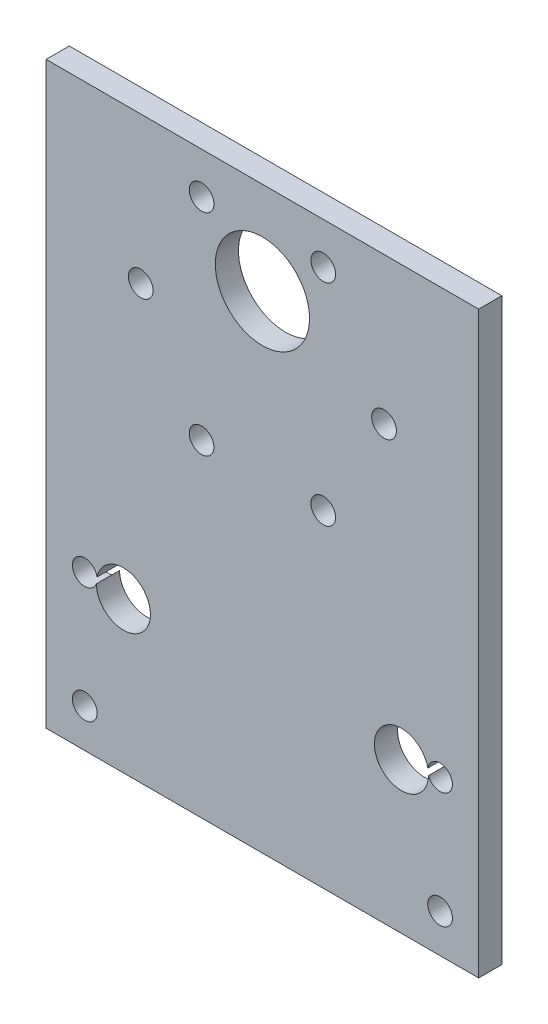
SolidWorks part; units mm, degrees
ref_plane "正面" through (0, 0, 0) normal (0, 0, 1) x (1, 0, 0)
ref_plane "平面" through (0, 0, 0) normal (0, 1, 0) x (1, 0, 0)
ref_plane "右側面" through (0, 0, 0) normal (1, 0, 0) x (0, 0, -1)
sketch "ｽｹｯﾁ1" plane through (0, 0, 0) normal (0, 0, 1) x (1, 0, 0)
  line L0 (0, 0) -> (0, 7)
  line L1 (-28, 12.5) -> (28, 12.5)
  line L2 (-28, 12.5) -> (-28, -12.5)
  line L3 (-28, -12.5) -> (28, -12.5)
  line L4 (28, 12.5) -> (28, -12.5)
  line L5 (-28, 12.5) -> (28, -12.5) construction
  line L6 (-28, -12.5) -> (28, 12.5) construction
  line L7 (0, 7) -> (18, 7)
  line L8 (0, 7) -> (-18, 7)
  circle A0 centre (-18, 7) radius 3.5
  circle A1 centre (18, 7) radius 3.5
  point P0 (0, 0)
  dimension "D3" = 7
  dimension "D4" = 7
  dimension "D1" = 18
  dimension "D2" = 18
  dimension "D5" = 25
  dimension "D6" = 56
  dimension "D7" = 7
extrude "ﾎﾞｽ - 押し出し1" add sketch "ｽｹｯﾁ1" along normal blind 3
sketch "ｽｹｯﾁ2" plane through (0, 0, 3) normal (0, 0, 1) x (1, 0, 0)
  line L0 (-28, 12.5) -> (-28, -12.5) construction
  line L1 (-28, 12.5) -> (-23, 12.5)
  line L2 (-28, 12.5) -> (-28, 7.5)
  line L3 (-28, 7.5) -> (-23, 7.5)
  line L4 (-23, 12.5) -> (-23, 7.5)
  line L5 (-28, -12.5) -> (-23, -12.5)
  line L6 (-28, -12.5) -> (-28, -7.5)
  line L7 (-28, -7.5) -> (-23, -7.5)
  line L8 (-23, -12.5) -> (-23, -7.5)
  line L9 (-28, -12.5) -> (28, -12.5) construction
  line L10 (28, 12.5) -> (28, -12.5) construction
  line L11 (28, -12.5) -> (23, -12.5)
  line L12 (28, -12.5) -> (28, -7.5)
  line L13 (28, -7.5) -> (23, -7.5)
  line L14 (23, -12.5) -> (23, -7.5)
  line L16 (28, 12.5) -> (23, 12.5)
  line L17 (28, 12.5) -> (28, 7.5)
  line L18 (28, 7.5) -> (23, 7.5)
  line L19 (23, 12.5) -> (23, 7.5)
  circle A0 centre (-23, 7.5) radius 1.6
  circle A1 centre (-23, -7.5) radius 1.6
  circle A2 centre (23, 7.5) radius 1.6
  circle A3 centre (23, -7.5) radius 1.6
  dimension "D9" = 3.2
  dimension "D10" = 3.2
  dimension "D11" = 3.2
  dimension "D12" = 3.2
  dimension "D1" = 5
  dimension "D2" = 5
  dimension "D3" = 5
  dimension "D4" = 5
  dimension "D5" = 5
  dimension "D6" = 5
  dimension "D7" = 5
  dimension "D8" = 5
extrude "ｶｯﾄ - 押し出し1" cut sketch "ｽｹｯﾁ2" against normal through all contours L3 A0 L4 | L4 A0 L3 | L7 A1 L8 | L8 A1 L7 | L18 A2 L19 | L19 A2 L18 | L14 A3 L13 | L13 A3 L14
sketch "ｽｹｯﾁ3" plane through (0, 12.5, 0) normal (0, 1, 0) x (1, 0, 0)
  line L0 (-28, 0) -> (28, 0) construction
  line L1 (-28, -3) -> (28, -3)
  line L2 (-28, -3) -> (-28, 0)
  line L3 (-28, 0) -> (28, 0)
  line L4 (28, -3) -> (28, 0)
  line L5 (28, -3) -> (28, 0) construction
extrude "ﾎﾞｽ - 押し出し2" add sketch "ｽｹｯﾁ3" along normal blind 50
sketch "ｽｹｯﾁ4" plane through (0, 0, 0) normal (0, 0, 1) x (1, 0, 0)
  line L0 (0, 62.5) -> (0, 43.5)
  line L1 (-28, 62.5) -> (28, 62.5) construction
  line L2 (0, 43.5) -> (7.875, 57.1399)
  line L3 (0, 43.5) -> (15.75, 43.5)
  line L4 (0, 43.5) -> (7.875, 29.8601)
  line L5 (0, 43.5) -> (-7.875, 29.8601)
  line L6 (0, 43.5) -> (-15.75, 43.5)
  line L7 (0, 43.5) -> (-7.875, 57.1399)
  line L8 (0, 43.5) -> (0, 50.5)
  circle A0 centre (0, 43.5) radius 15.75
  circle A1 centre (-7.875, 57.1399) radius 1.6
  circle A2 centre (7.875, 57.1399) radius 1.6
  circle A3 centre (15.75, 43.5) radius 1.6
  circle A4 centre (7.875, 29.8601) radius 1.6
  circle A5 centre (-7.875, 29.8601) radius 1.6
  circle A6 centre (-15.75, 43.5) radius 1.6
  circle A7 centre (0, 50.5) radius 6.1
  dimension "D1" = 31.5
  dimension "D8" = 3.2
  dimension "D9" = 3.2
  dimension "D10" = 3.2
  dimension "D11" = 3.2
  dimension "D12" = 3.2
  dimension "D13" = 3.2
  dimension "D15" = 12.2
  dimension "D2" = 19
  dimension "D3" = 30
  dimension "D4" = 60
  dimension "D5" = 60
  dimension "D6" = 60
  dimension "D7" = 30
  dimension "D14" = 7
extrude "ｶｯﾄ - 押し出し4" cut sketch "ｽｹｯﾁ4" along normal blind 40 contours A0 A2 | A0 A2 L2 | L2 A2 A0 | A0 A3 | A0 A3 L3 | L2 A7 L0 | L0 A7 L7 | L2 A7 | L7 A7 | A0 A1 | L7 A1 A0 | A0 A1 L7 | A0 A6 | L6 A6 A0 | A0 A6 L6 | A0 A4 | A0 A4 L4 | A0 A5 L5 | L5 A5 A0 | A0 A5 | L3 A3 A0
